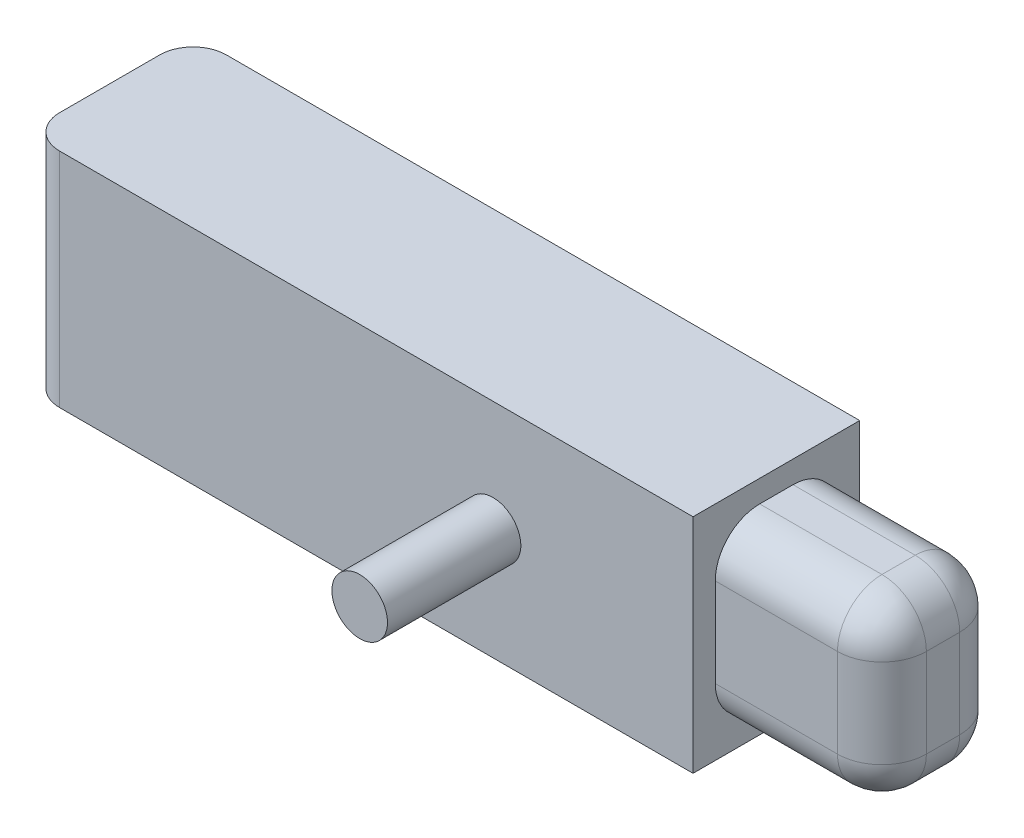
SolidWorks part; units mm, degrees
ref_plane "Alzado" through (0, 0, 0) normal (0, 0, 1) x (1, 0, 0)
ref_plane "Planta" through (0, 0, 0) normal (0, 1, 0) x (1, 0, 0)
ref_plane "Vista lateral" through (0, 0, 0) normal (1, 0, 0) x (0, 0, -1)
sketch "Croquis1" plane through (0, 0, 0) normal (0, 1, 0) x (1, 0, 0)
  line L1 (30, -7.5) -> (-30, -7.5)
  line L2 (30, -7.5) -> (30, 7.5)
  line L3 (30, 7.5) -> (-30, 7.5)
  line L4 (-30, -7.5) -> (-30, 7.5)
  line L5 (30, -7.5) -> (-30, 7.5) construction
  line L6 (30, 7.5) -> (-30, -7.5) construction
  point P0 (0, 0)
  dimension "D1" = 60
  dimension "D2" = 15
extrude "Saliente-Extruir1" add sketch "Croquis1" along normal blind 20
sketch "Croquis2" plane through (0, 0, 7.5) normal (0, 0, 1) x (1, 0, 0)
  line L0 (-30, 20) -> (-30, 0) construction
  line L1 (-30, 20) -> (30, 20) construction
  line L6 (30, 20) -> (30, 0) construction
  circle A0 centre (12, 10) radius 2.5
  point P6 (-30, 10)
  dimension "D1" = 5
  dimension "D2" = 18
  dimension "D3" = 10
extrude "Saliente-Extruir2" add sketch "Croquis2" along normal blind 12
sketch "Croquis3" plane through (30, 0, 0) normal (1, 0, 0) x (0, 0, -1)
  line L0 (-7.5, 20) -> (7.5, 20) construction
  line L1 (5.5, 2) -> (-5.5, 2)
  line L2 (5.5, 2) -> (5.5, 18)
  line L3 (5.5, 18) -> (-5.5, 18)
  line L4 (-5.5, 2) -> (-5.5, 18)
  line L5 (5.5, 2) -> (-5.5, 18) construction
  line L6 (5.5, 18) -> (-5.5, 2) construction
  line L7 (-7.5, 0) -> (7.5, 0) construction
  line L8 (-7.5, 20) -> (-7.5, 0) construction
  line L9 (7.5, 20) -> (7.5, 0) construction
  point P0 (0, 10)
  dimension "D1" = 2
  dimension "D2" = 2
  dimension "D3" = 2
  dimension "D4" = 2
extrude "Saliente-Extruir3" add sketch "Croquis3" along normal blind 15
fillet "Redondeo1" radius 4 4 edges at (37.5, 18, -5.5) (37.5, 2, -5.5) (37.5, 2, 5.5) (37.5, 18, 5.5)
fillet "Redondeo2" radius 4 8 edges at (45, 3.1716, -4.3284) (45, 2, 0) (45, 3.1716, 4.3284) (45, 10, 5.5) (45, 16.8284, 4.3284) (45, 18, 0) (45, 16.8284, -4.3284) (45, 10, -5.5)
fillet "Redondeo3" radius 3 2 edges at (-30, 10, -7.5) (-30, 10, 7.5)
sketch "Croquis4" plane through (0, 0, 7.5) normal (0, 0, 1) x (1, 0, 0)
scale "Escala1" scale about centroid uniform scaling yes scale factor 2
